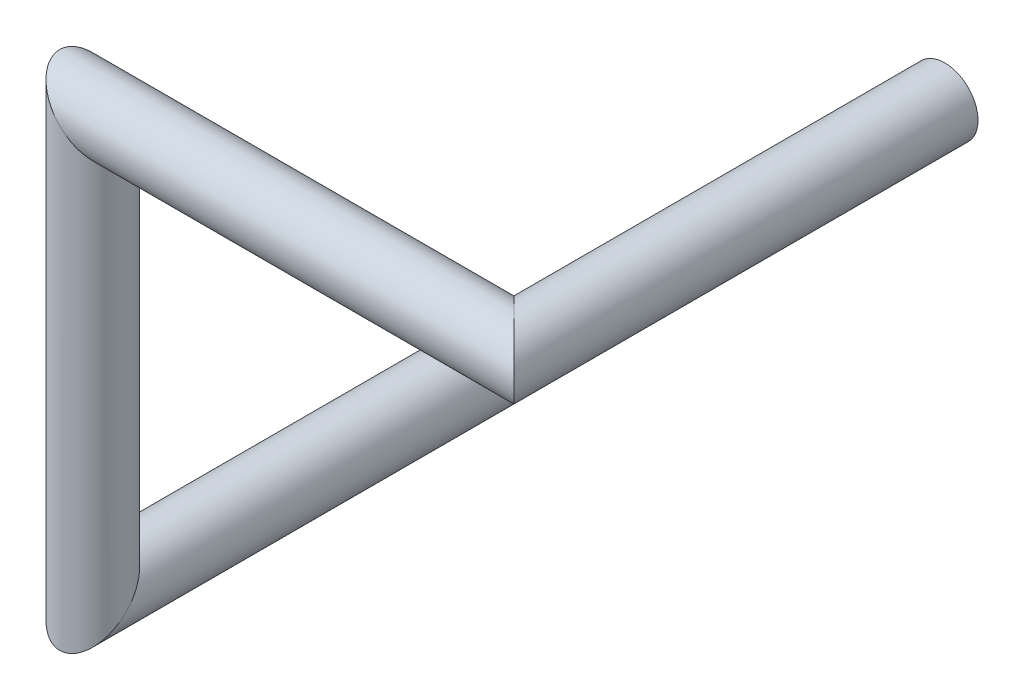
SolidWorks part; units mm, degrees
ref_plane "Front Plane" through (0, 0, 0) normal (0, 0, 1) x (1, 0, 0)
ref_plane "Top Plane" through (0, 0, 0) normal (0, 1, 0) x (1, 0, 0)
ref_plane "Right Plane" through (0, 0, 0) normal (1, 0, 0) x (0, 0, -1)
sketch3d "3DSketch3"
  line L0 (0, 0, 0) -> (0, 0, 2.6)
  line L1 (0, 0, 2.6) -> (0, 2.54, 2.6)
  line L2 (0, 2.54, 2.6) -> (2.54, 2.54, 2.6)
  line L3 (2.54, 2.54, 2.6) -> (2.54, 2.54, 0)
  dimension "D2" = 2.6
  dimension "D1" = 2.6
  dimension "D3" = 2.54
  dimension "D4" = 2.54
sweep "Sweep1" add path "3DSketch3" circular profile diameter 0.4 parameters "D3"=0.4
equation "\"D2@3DSketch3\"=\"D1@3DSketch3\""
